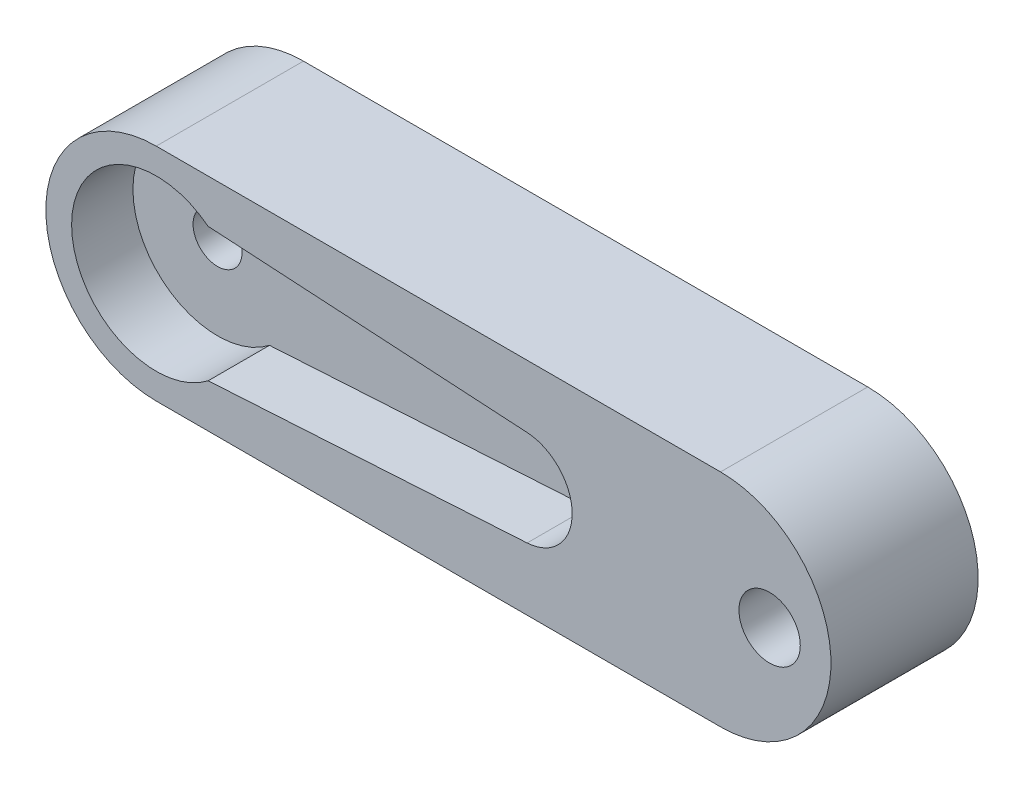
SolidWorks part; units mm, degrees
material "ABS"
ref_plane "Front Plane" through (0, 0, 0) normal (0, 0, 1) x (1, 0, 0)
ref_plane "Top Plane" through (0, 0, 0) normal (0, 1, 0) x (1, 0, 0)
ref_plane "Right Plane" through (0, 0, 0) normal (1, 0, 0) x (0, 0, -1)
sketch "Sketch1" plane through (0, 0, 0) normal (0, 0, 1) x (1, 0, 0)
  line L0 (0, 0) -> (23, 0) construction
  line L1 (0, 4.5) -> (23, 4.5)
  line L2 (0, -4.5) -> (23, -4.5)
  arc A0 (0, 4.5) -> (0, -4.5) centre (0, 0) ccw
  arc A1 (23, -4.5) -> (23, 4.5) centre (23, 0) ccw
  point P3 (11.5, 0)
  point P8 (25, 0)
  point P9 (27.5, 0)
  dimension "D1" = 2.5
  dimension "D2" = 9
  dimension "D3" = 25
extrude "Boss-Extrude1" add sketch "Sketch1" along normal blind 6
sketch "Sketch2" plane through (0, 0, 6) normal (0, 0, 1) x (1, 0, 0)
  line L0 (0, 0) -> (16.9535, 0) construction
  line L1 (2.1159, 2.725) -> (15.1162, 1.95)
  line L2 (2.1159, -2.725) -> (15.1162, -1.95)
  arc A0 (2.1159, 2.725) -> (2.1159, -2.725) centre (0, 0) ccw
  arc A1 (15.1162, 1.95) -> (15.1162, -1.95) centre (15, 0) cw
  dimension "D1" = 6.9
  dimension "D2" = 5.45
  dimension "D3" = 15
  dimension "D4" = 3.9
extrude "Cut-Extrude1" cut sketch "Sketch2" against normal blind 2.5
sketch "Sketch3" plane through (0, 0, 6) normal (0, 0, 1) x (1, 0, 0)
  circle A0 centre (0, 0) radius 1
  dimension "D1" = 2
extrude "Cut-Extrude2" cut sketch "Sketch3" against normal through all
sketch "Sketch4" plane through (0, 0, 0) normal (0, 0, -1) x (-1, 0, 0)
  circle A0 centre (0, 0) radius 2
  dimension "D1" = 4
extrude "Cut-Extrude3" cut sketch "Sketch4" against normal blind 1.5
sketch "Sketch5" plane through (0, 0, 6) normal (0, 0, 1) x (1, 0, 0)
  circle A0 centre (25, 0) radius 1.25
  arc A1 (23, -4.5) -> (23, 4.5) centre (23, 0) ccw construction
  point P2 (27.5, 0)
  point P3 (26.25, 0)
  dimension "D1" = 2.5
  dimension "D2" = 2.5
extrude "Cut-Extrude4" cut sketch "Sketch5" against normal through all
chamfer "Chamfer1" [suppressed] distance 1 angle 45
